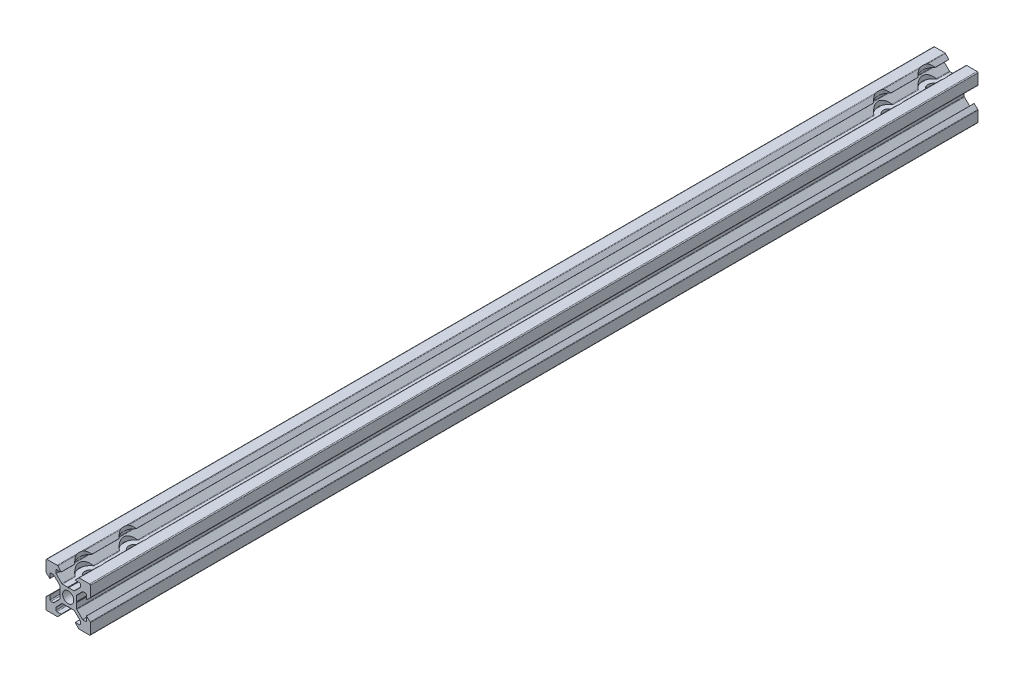
SolidWorks part; units mm, degrees
material "6063-T5"
ref_plane "前视基准面" through (0, 0, 0) normal (0, 0, 1) x (1, 0, 0)
ref_plane "上视基准面" through (0, 0, 0) normal (0, 1, 0) x (1, 0, 0)
ref_plane "右视基准面" through (0, 0, 0) normal (1, 0, 0) x (0, 0, -1)
sketch "草图1" plane through (0, 0, 0) normal (0, 0, 1) x (1, 0, 0)
  line L0 (0, 0) -> (13486.7145, 0) construction
  line L1 (0, 0) -> (0, 13486.7145) construction
  line L2 (0, 0) -> (9536.5473, 9536.5473) construction
  line L3 (0.2, 3.8) -> (2.5737, 3.8)
  line L4 (2.8565, 3.9172) -> (5.3828, 6.4435)
  line L5 (5.5, 6.7263) -> (5.5, 7.8)
  line L6 (5.1, 8.2) -> (3.2, 8.2)
  line L7 (3.1681, 8.2732) -> (4.6563, 9.8725)
  line L8 (4.9492, 10) -> (9.6, 10)
  line L9 (3.8, 0.2) -> (3.8, 2.5737)
  line L10 (3.9172, 2.8565) -> (6.4435, 5.3828)
  line L11 (6.7263, 5.5) -> (7.8, 5.5)
  line L12 (8.2, 5.1) -> (8.2, 3.2)
  line L13 (8.2732, 3.1681) -> (9.8725, 4.6563)
  line L14 (10, 4.9492) -> (10, 9.6)
  line L15 (3.8, -0.2) -> (3.8, -2.5737)
  line L16 (3.9172, -2.8565) -> (6.4435, -5.3828)
  line L17 (6.7263, -5.5) -> (7.8, -5.5)
  line L18 (8.2, -5.1) -> (8.2, -3.2)
  line L19 (8.2732, -3.1681) -> (9.8725, -4.6563)
  line L20 (10, -4.9492) -> (10, -9.6)
  line L21 (4.9492, -10) -> (9.6, -10)
  line L22 (3.1681, -8.2732) -> (4.6563, -9.8725)
  line L23 (5.1, -8.2) -> (3.2, -8.2)
  line L24 (5.5, -6.7263) -> (5.5, -7.8)
  line L25 (2.8565, -3.9172) -> (5.3828, -6.4435)
  line L26 (0.2, -3.8) -> (2.5737, -3.8)
  line L27 (-0.2, -3.8) -> (-2.5737, -3.8)
  line L28 (-2.8565, -3.9172) -> (-5.3828, -6.4435)
  line L29 (-5.5, -6.7263) -> (-5.5, -7.8)
  line L30 (-5.1, -8.2) -> (-3.2, -8.2)
  line L31 (-3.1681, -8.2732) -> (-4.6563, -9.8725)
  line L32 (-4.9492, -10) -> (-9.6, -10)
  line L33 (-10, -4.9492) -> (-10, -9.6)
  line L34 (-8.2732, -3.1681) -> (-9.8725, -4.6563)
  line L35 (-8.2, -5.1) -> (-8.2, -3.2)
  line L36 (-6.7263, -5.5) -> (-7.8, -5.5)
  line L37 (-3.9172, -2.8565) -> (-6.4435, -5.3828)
  line L38 (-3.8, -0.2) -> (-3.8, -2.5737)
  line L39 (-3.8, 0.2) -> (-3.8, 2.5737)
  line L40 (-3.9172, 2.8565) -> (-6.4435, 5.3828)
  line L41 (-6.7263, 5.5) -> (-7.8, 5.5)
  line L42 (-8.2, 5.1) -> (-8.2, 3.2)
  line L43 (-8.2732, 3.1681) -> (-9.8725, 4.6563)
  line L44 (-10, 4.9492) -> (-10, 9.6)
  line L45 (-4.9492, 10) -> (-9.6, 10)
  line L46 (-3.1681, 8.2732) -> (-4.6563, 9.8725)
  line L47 (-5.1, 8.2) -> (-3.2, 8.2)
  line L48 (-5.5, 6.7263) -> (-5.5, 7.8)
  line L49 (-2.8565, 3.9172) -> (-5.3828, 6.4435)
  line L50 (-0.2, 3.8) -> (-2.5737, 3.8)
  line L51 (-3.2, 8.2) -> (-3.1681, 8.2732)
  line L52 (3.2, 8.2) -> (3.1681, 8.2732)
  line L53 (-8.2, 3.2) -> (-8.2732, 3.1681)
  line L54 (8.2, 3.2) -> (8.2732, 3.1681)
  line L55 (8.2, -3.2) -> (8.2732, -3.1681)
  line L56 (3.2, -8.2) -> (3.1681, -8.2732)
  line L57 (-3.2, -8.2) -> (-3.1681, -8.2732)
  line L58 (-8.2, -3.2) -> (-8.2732, -3.1681)
  line L59 (-0.2, 3.8) -> (0, 3.6)
  line L60 (0, 3.6) -> (0.2, 3.8)
  line L61 (3.8, 0.2) -> (3.6, 0)
  line L62 (3.6, 0) -> (3.8, -0.2)
  line L63 (0.2, -3.8) -> (0, -3.6)
  line L64 (0, -3.6) -> (-0.2, -3.8)
  line L65 (-3.8, -0.2) -> (-3.6, 0)
  line L66 (-3.6, 0) -> (-3.8, 0.2)
  arc A0 (-4.9492, 10) -> (-4.6563, 9.8725) centre (-4.9492, 9.6) cw
  arc A1 (-5.1, 8.2) -> (-5.5, 7.8) centre (-5.1, 7.8) ccw
  arc A2 (-5.5, 6.7263) -> (-5.3828, 6.4435) centre (-5.1, 6.7263) ccw
  arc A3 (-2.8565, 3.9172) -> (-2.5737, 3.8) centre (-2.5737, 4.2) ccw
  arc A4 (-10, 9.6) -> (-9.6, 10) centre (-9.6, 9.6) cw
  arc A5 (-9.8725, 4.6563) -> (-10, 4.9492) centre (-9.6, 4.9492) cw
  arc A6 (-7.8, 5.5) -> (-8.2, 5.1) centre (-7.8, 5.1) ccw
  arc A7 (-6.4435, 5.3828) -> (-6.7263, 5.5) centre (-6.7263, 5.1) ccw
  arc A8 (-3.8, 2.5737) -> (-3.9172, 2.8565) centre (-4.2, 2.5737) ccw
  arc A9 (-10, -4.9492) -> (-9.8725, -4.6563) centre (-9.6, -4.9492) cw
  arc A10 (-8.2, -5.1) -> (-7.8, -5.5) centre (-7.8, -5.1) ccw
  arc A11 (-6.7263, -5.5) -> (-6.4435, -5.3828) centre (-6.7263, -5.1) ccw
  arc A12 (-3.9172, -2.8565) -> (-3.8, -2.5737) centre (-4.2, -2.5737) ccw
  arc A13 (-9.6, -10) -> (-10, -9.6) centre (-9.6, -9.6) cw
  arc A14 (-4.6563, -9.8725) -> (-4.9492, -10) centre (-4.9492, -9.6) cw
  arc A15 (-5.5, -7.8) -> (-5.1, -8.2) centre (-5.1, -7.8) ccw
  arc A16 (-5.3828, -6.4435) -> (-5.5, -6.7263) centre (-5.1, -6.7263) ccw
  arc A17 (-2.5737, -3.8) -> (-2.8565, -3.9172) centre (-2.5737, -4.2) ccw
  arc A18 (4.9492, -10) -> (4.6563, -9.8725) centre (4.9492, -9.6) cw
  arc A19 (5.1, -8.2) -> (5.5, -7.8) centre (5.1, -7.8) ccw
  arc A20 (5.5, -6.7263) -> (5.3828, -6.4435) centre (5.1, -6.7263) ccw
  arc A21 (2.8565, -3.9172) -> (2.5737, -3.8) centre (2.5737, -4.2) ccw
  arc A22 (10, -9.6) -> (9.6, -10) centre (9.6, -9.6) cw
  arc A23 (9.8725, -4.6563) -> (10, -4.9492) centre (9.6, -4.9492) cw
  arc A24 (7.8, -5.5) -> (8.2, -5.1) centre (7.8, -5.1) ccw
  arc A25 (6.4435, -5.3828) -> (6.7263, -5.5) centre (6.7263, -5.1) ccw
  arc A26 (3.8, -2.5737) -> (3.9172, -2.8565) centre (4.2, -2.5737) ccw
  arc A27 (9.8725, 4.6563) -> (10, 4.9492) centre (9.6, 4.9492) ccw
  arc A28 (7.8, 5.5) -> (8.2, 5.1) centre (7.8, 5.1) cw
  arc A29 (6.4435, 5.3828) -> (6.7263, 5.5) centre (6.7263, 5.1) cw
  arc A30 (3.8, 2.5737) -> (3.9172, 2.8565) centre (4.2, 2.5737) cw
  arc A31 (9.6, 10) -> (10, 9.6) centre (9.6, 9.6) cw
  arc A32 (4.6563, 9.8725) -> (4.9492, 10) centre (4.9492, 9.6) cw
  arc A33 (5.5, 7.8) -> (5.1, 8.2) centre (5.1, 7.8) ccw
  arc A34 (5.3828, 6.4435) -> (5.5, 6.7263) centre (5.1, 6.7263) ccw
  arc A35 (2.5737, 3.8) -> (2.8565, 3.9172) centre (2.5737, 4.2) ccw
  circle A36 centre (0, 0) radius 2
  point P12 (3.1, 8.2)
  point P18 (8.2, 3.1)
  point P28 (8.2, -3.1)
  point P34 (3.1, -8.2)
  point P41 (-3.1, -8.2)
  point P47 (-8.2, -3.1)
  point P54 (-8.2, 3.1)
  point P60 (-3.1, 8.2)
  point P62 (0, 0)
  point P112 (10, 4.775)
  point P115 (8.2, 5.5)
  point P118 (6.5607, 5.5)
  point P121 (3.8, 2.7393)
  point P124 (10, 10)
  point P127 (4.775, 10)
  point P130 (5.5, 8.2)
  point P133 (5.5, 6.5607)
  point P136 (2.7393, 3.8)
  point P168 (0, 0)
  dimension "D9" = 0.4
  dimension "D23" = 4
  dimension "D1" = 5.5
  dimension "D2" = 10
  dimension "D3" = 3.1
  dimension "D4" = 1.5
  dimension "D5" = 1.8
  dimension "D7" = 7.6
  dimension "D11" = 20
  dimension "D12" = 45
  dimension "D13" = 0.4
  dimension "D8" = 4
  dimension "D14" = 4
extrude "凸台-拉伸1" add sketch "草图1" along normal blind 400
hole_wizard "Ø5.2 (5.2) 直径孔1" positions "草图4" profile "草图5" hole size "Ø5.2" standard "GB" end condition through all
sketch "草图4" plane through (0, 10, 0) normal (0, 1, 0) x (1, 0, 0)
  line L0 (0, -400) -> (0, 0) construction
  line L1 (9.6, 0) -> (4.9492, 0) construction
  line L2 (9.6, -400) -> (4.9492, -400) construction
  point P0 (0, -10)
  point P2 (0, -30)
  point P4 (0, -390)
  point P6 (0, -370)
  dimension "D1" = 10
  dimension "D2" = 20
  dimension "D3" = 10
  dimension "D4" = 20
sketch "草图5" plane through (0, 10, 10) normal (1, 0, 0) x (0, 0, 1)
  line L0 (0, 0) -> (0, 20)
  line L1 (0, 20) -> (2.6, 20)
  line L2 (2.6, 20) -> (2.6, 0)
  line L5 (2.6, 0) -> (0, 0)
  line L11 (0, -6.35) -> (0, 107.95) construction
  dimension "通孔孔直径" = 5.2
  dimension "通孔孔深度" = 20
hole_wizard "Ø10.0 (10) 直径孔1" positions "草图6" profile "草图7" hole size "Ø10.0" standard "GB"
sketch "草图6" plane through (0, 10, 0) normal (0, 1, 0) x (1, 0, 0)
  point P0 (0, -390)
  point P3 (0, -370)
  point P6 (0, -30)
  point P9 (0, -10)
sketch "草图7" plane through (0, 10, 390) normal (1, 0, 0) x (0, 0, 1)
  line L0 (0, 0) -> (0, 6.2)
  line L1 (0, 6.2) -> (5, 6.2)
  line L2 (5, 6.2) -> (5, 0)
  line L5 (5, 0) -> (0, 0)
  line L10 (0, 6.2) -> (-5, 6.2) construction
  line L11 (0, -6.35) -> (0, 107.95) construction
  dimension "孔直径" = 10
  dimension "孔深度" = 6.2
  dimension "导头角度" = 180
hole_wizard "Ø5.0 (5) 直径孔1" positions "草图8" profile "草图9" hole size "Ø5.0" standard "GB"
sketch "草图8" plane through (0, 0, 400) normal (0, 0, 1) x (1, 0, 0)
  point P0 (0, 0)
sketch "草图9" plane through (0, 0, 400) normal (1, 0, 0) x (0, -1, 0)
  line L0 (0, 0) -> (0, 11.5022)
  line L1 (0, 11.5022) -> (2.5, 10)
  line L2 (2.5, 10) -> (2.5, 0)
  line L5 (2.5, 0) -> (0, 0)
  line L10 (0, 11.5022) -> (-2.5, 10) construction
  line L11 (0, -6.35) -> (0, 107.95) construction
  dimension "孔直径" = 5
  dimension "孔深度" = 10
  dimension "导头角度" = 118
hole_wizard "Ø5.0 (5) 直径孔2" positions "草图10" profile "草图11" hole size "Ø5.0" standard "GB"
sketch "草图10" plane through (0, 0, 0) normal (0, 0, -1) x (-1, 0, 0)
  point P0 (0, 0)
sketch "草图11" plane through (0, 0, 0) normal (1, 0, 0) x (0, 1, 0)
  line L0 (0, 0) -> (0, 11.5022)
  line L1 (0, 11.5022) -> (2.5, 10)
  line L2 (2.5, 10) -> (2.5, 0)
  line L5 (2.5, 0) -> (0, 0)
  line L10 (0, 11.5022) -> (-2.5, 10) construction
  line L11 (0, -6.35) -> (0, 107.95) construction
  dimension "孔直径" = 5
  dimension "孔深度" = 10
  dimension "导头角度" = 118
